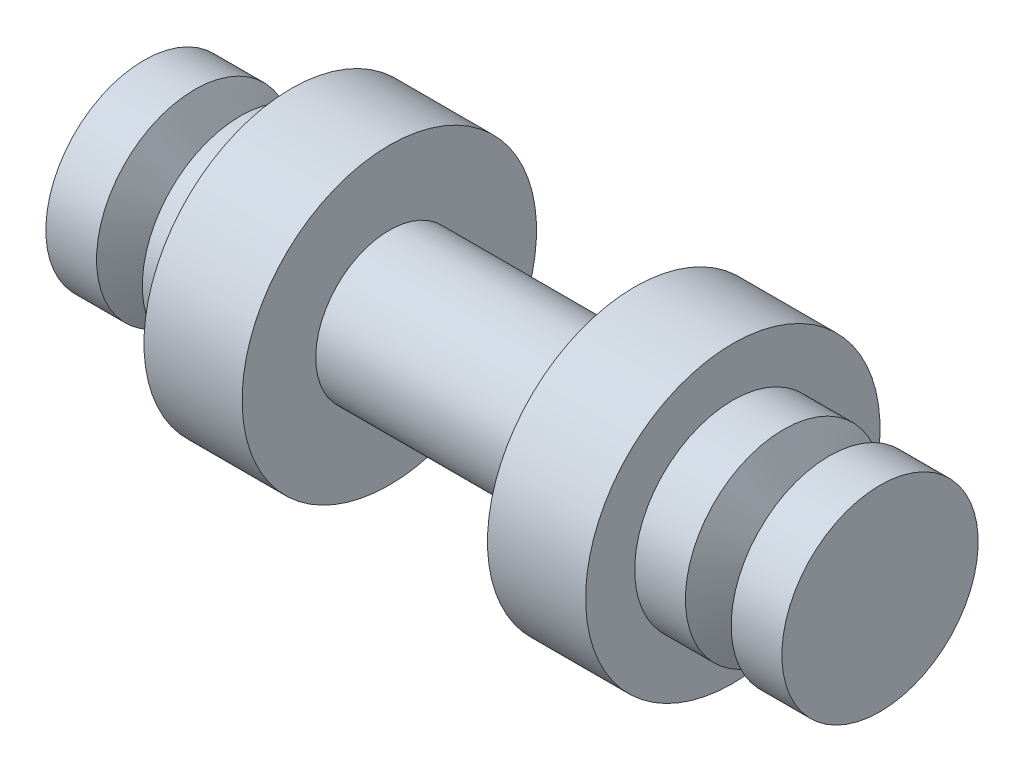
SolidWorks part; units mm, degrees
ref_plane "정면" through (0, 0, 0) normal (0, 0, 1) x (1, 0, 0)
ref_plane "윗면" through (0, 0, 0) normal (0, 1, 0) x (1, 0, 0)
ref_plane "우측면" through (0, 0, 0) normal (1, 0, 0) x (0, 0, -1)
sketch "스케치1" plane through (0, 0, 0) normal (0, 0, 1) x (1, 0, 0)
  line L0 (-75, 0) -> (75, 0) construction
  line L1 (25, 15) -> (-25, 15)
  line L2 (0, 38.5192) -> (0, -27.6895) construction
  line L3 (-75, 20) -> (-75, 0)
  line L4 (-64.6631, 20) -> (-75, 20)
  line L5 (-60, 10) -> (-64.6631, 20)
  line L6 (-55.3369, 20) -> (-60, 10)
  line L7 (-45, 20) -> (-55.3369, 20)
  line L8 (-45, 30) -> (-45, 20)
  line L9 (25, 15) -> (25, 30)
  line L10 (25, 30) -> (45, 30)
  line L11 (45, 30) -> (45, 20)
  line L12 (45, 20) -> (55.3369, 20)
  line L13 (55.3369, 20) -> (60, 10)
  line L14 (60, 10) -> (64.6631, 20)
  line L15 (64.6631, 20) -> (75, 20)
  line L16 (75, 20) -> (75, 0)
  line L17 (60, 10) -> (60, 0) construction
  line L18 (-25, 30) -> (-45, 30)
  line L19 (-25, 15) -> (-25, 30)
  line L20 (-75, 0) -> (75, 0)
  point P25 (0, 15)
  dimension "D1" = 310
  dimension "D2" = 15
  dimension "D3" = 10
  dimension "D4" = 40
  dimension "D5" = 60
  dimension "D6" = 50
  dimension "D7" = 90
  dimension "D8" = 150
  dimension "D9" = 30
revolve "회전1" add sketch "스케치1" angle 360 about L20
